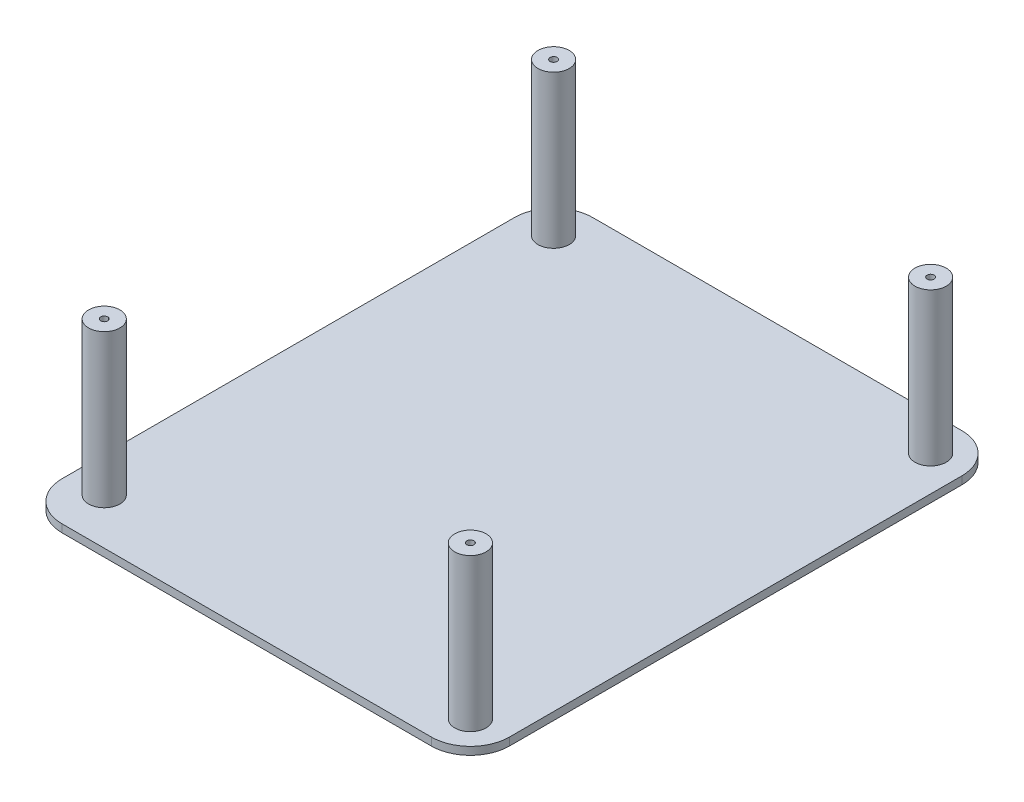
SolidWorks part; units mm, degrees
ref_plane "Спереди" through (0, 0, 0) normal (0, 0, 1) x (1, 0, 0)
ref_plane "Сверху" through (0, 0, 0) normal (0, 1, 0) x (1, 0, 0)
ref_plane "Справа" through (0, 0, 0) normal (1, 0, 0) x (0, 0, -1)
sketch "Эскиз1" plane through (0, 0, 0) normal (0, 1, 0) x (1, 0, 0)
  line L1 (-57.435, 52.5896) -> (56.9622, 52.5896)
  line L2 (-57.435, 52.5896) -> (-57.435, -83.0798)
  line L3 (-57.435, -83.0798) -> (56.9622, -83.0798)
  line L4 (56.9622, 52.5896) -> (56.9622, -83.0798)
extrude "Бобышка-Вытянуть1" add sketch "Эскиз1" along normal blind 2
sketch "Эскиз2" plane through (0, 2, 0) normal (0, 1, 0) x (1, 0, 0)
  line L0 (56.9622, 52.5896) -> (-57.435, 52.5896) construction
  line L1 (-57.435, 52.5896) -> (-57.435, -83.0798) construction
  line L2 (56.9622, -83.0798) -> (56.9622, 52.5896) construction
  line L3 (-57.435, -83.0798) -> (56.9622, -83.0798) construction
  circle A0 centre (-48.435, 43.5896) radius 4
  circle A1 centre (47.9622, 43.5896) radius 4
  circle A2 centre (47.9622, -74.0798) radius 4
  circle A3 centre (-48.435, -71.3067) radius 4
  dimension "D1" = 9
  dimension "D2" = 9
  dimension "D3" = 9
  dimension "D4" = 9
  dimension "D5" = 9
  dimension "D6" = 9
  dimension "D7" = 11.7731
  dimension "D8" = 9
extrude "Бобышка-Вытянуть2" add sketch "Эскиз2" along normal blind 39
sketch "Эскиз3" plane through (0, 41, 0) normal (0, 1, 0) x (1, 0, 0)
  circle A0 centre (47.9622, -74.0798) radius 0.9
  circle A1 centre (-48.435, -71.3067) radius 0.9
  circle A2 centre (-48.435, 43.5896) radius 0.9
  circle A3 centre (47.9622, 43.5896) radius 0.9
extrude "Вырез-Вытянуть1" cut sketch "Эскиз3" against normal blind 11
fillet "Скругление1" radius 10 4 edges at (-57.435, 1, 83.0798) (-57.435, 1, -52.5896) (56.9622, 1, -52.5896) (56.9622, 1, 83.0798)
